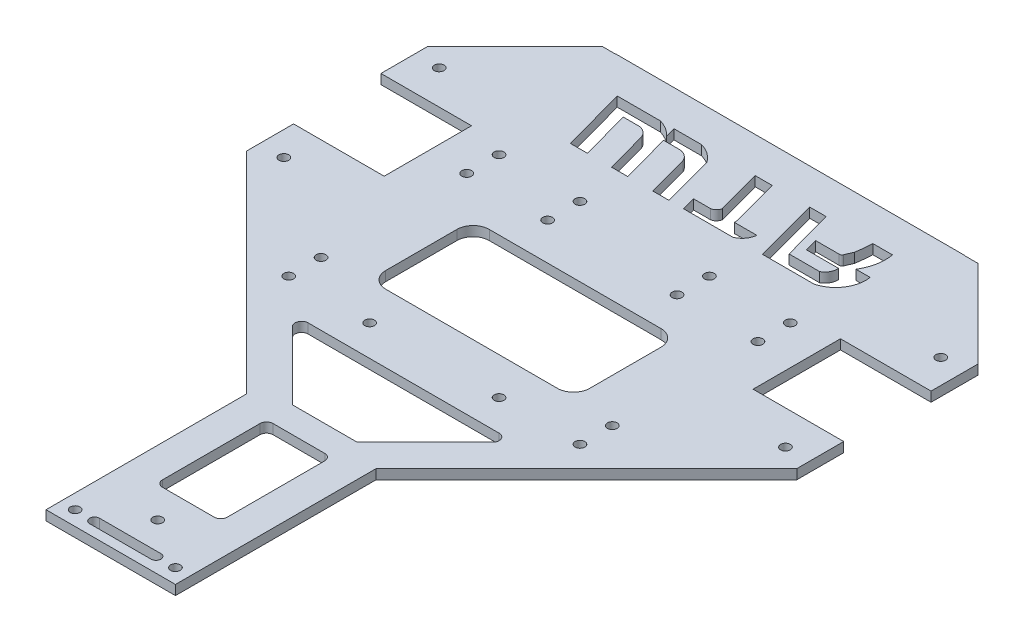
SolidWorks part; units mm, degrees
ref_plane "前视基准面" through (0, 0, 0) normal (0, 0, 1) x (1, 0, 0)
ref_plane "上视基准面" through (0, 0, 0) normal (0, 1, 0) x (1, 0, 0)
ref_plane "右视基准面" through (0, 0, 0) normal (1, 0, 0) x (0, 0, -1)
sketch "草图1" plane through (0, 0, 0) normal (0, 1, 0) x (1, 0, 0)
  line L0 (85, -28) -> (58, -55)
  line L1 (-85, -24) -> (85, -24)
  line L2 (-85, -24) -> (-85, 24)
  line L3 (-85, 24) -> (85, 24)
  line L4 (85, -24) -> (85, 24)
  line L5 (-85, -24) -> (85, 24) construction
  line L6 (-85, 24) -> (85, -24) construction
  line L7 (85, 13.5) -> (57, 13.5)
  line L8 (85, 13.5) -> (85, -13.5)
  line L9 (85, -13.5) -> (57, -13.5)
  line L10 (57, 13.5) -> (57, -13.5)
  line L11 (58, -55) -> (-58, -55)
  line L12 (0, -60) -> (0, 24)
  line L13 (65, 13.5) -> (65, -13.5)
  line L14 (85, 18.6302) -> (50, 18.6302)
  line L15 (50, 18.6302) -> (-50, 18.6302)
  line L16 (-85, -24) -> (-85, -28)
  line L17 (-85, -13.5) -> (-57, -13.5)
  line L18 (-57, 13.5) -> (-57, -13.5)
  line L19 (-65, 13.5) -> (-65, -13.5)
  line L20 (-85, 13.5) -> (-57, 13.5)
  line L21 (-85, 18.6302) -> (-50, 18.6302)
  line L22 (0, 0) -> (27.7736, 0)
  line L23 (85, -24) -> (85, -28)
  line L24 (-85, -28) -> (-58, -55)
  line L25 (85, 13.5) -> (85, 28)
  line L26 (85, 28) -> (85, 55)
  line L27 (85, 55) -> (-85, 55)
  line L28 (-85, 55) -> (-85, 24)
  line L29 (-85, 24) -> (-54, 55)
  line L30 (85, 24) -> (54, 55)
  circle A2 centre (77.5, 24) radius 1.5
  circle A3 centre (77.5, -24) radius 1.5
  circle A4 centre (-77.5, -24) radius 1.5
  circle A5 centre (-77.5, 24) radius 1.5
  point P0 (0, 0)
  point P34 (0, 18.6302)
  point P38 (85, 0)
  point P42 (0, -55)
  dimension "D4" = 3
  dimension "D5" = 7.5
  dimension "D7" = 7.5
  dimension "D8" = 3
  dimension "D1" = 48
  dimension "D2" = 27
  dimension "D3" = 28
  dimension "D6" = 10.5
  dimension "D9" = 20
  dimension "D10" = 35
  dimension "D11" = 50
  dimension "D12" = 45
  dimension "D13" = 55
  dimension "D14" = 28
  dimension "D15" = 28
  dimension "D16" = 55
  dimension "D17" = 45
extrude "凸台-拉伸1" add sketch "草图1" along normal blind 3
sketch "草图2" plane through (0, 3, 0) normal (0, 1, 0) x (1, 0, 0)
  line L0 (0, 0) -> (85, 0)
  line L1 (85, 0) -> (85, 28)
  line L2 (85, 28) -> (58.0785, 54.9215)
  line L3 (58.0785, 54.9215) -> (-58.0785, 54.9215)
  line L4 (-58.0785, 54.9215) -> (-85, 28)
  line L5 (-85, 28) -> (-85, 0)
  line L6 (-85, 0) -> (0, 0)
  line L7 (85, 13.5) -> (-85, 13.5)
  line L8 (-85, 13.5) -> (-57, 13.5) construction
  line M12 (57, 13.5) -> (85, 13.5)
  line M13 (85, 13.5) -> (85, 24)
  line M14 (85, 24) -> (54, 55)
  line M16 (-54, 55) -> (-85, 24)
  line M17 (-85, 24) -> (-85, 13.5)
  line M18 (-85, 13.5) -> (-57, 13.5)
  circle M24 centre (-77.5, 24) radius 1.5
  circle M25 centre (77.5, 24) radius 1.5
  dimension "D1" = 28
  dimension "D2" = 28
  dimension "D3" = 45
  dimension "D4" = 45
extrude "凸台-拉伸2" add sketch "草图2" against normal blind 3 contours L7 L3 M12 M13 M14 M16 M17 M18 M24 M25 | L4 L5 L3 M16 | L2 L3 L1 M14
sketch "草图3" plane through (0, 0, 0) normal (0, -1, 0) x (1, 0, 0)
  line L0 (-58, 55) -> (-58, 155)
  line L1 (-58, 155) -> (58, 155)
  line L2 (58, 155) -> (58, 55)
  line L3 (58, 55) -> (-58, 55) construction
  line L4 (58, 155) -> (-58, 55)
  line L5 (0, 55) -> (20, 55)
  line L6 (20, 55) -> (-20, 55)
  line L7 (20, 55) -> (20, 155)
  line L8 (20, 155) -> (-20, 155)
  line L9 (-20, 155) -> (-20, 55)
  line L10 (58, 55) -> (20, 93)
  line L11 (58, 55) -> (-58, 55) construction
  line L12 (-58, 55) -> (-20, 93)
  line M19 (58, 55) -> (-58, 55)
  dimension "D1" = 100
  dimension "D2" = 20
  dimension "D3" = 20
  dimension "D4" = 45
  dimension "D5" = 45
extrude "凸台-拉伸6" add sketch "草图3" against normal blind 3 contours L1 L9 L4 L7 | L4 L9 L7 M19 | L10 L7 M19 | L9 L4 M19 | L12 L4 L9
sketch "草图4" plane through (0, 0, 0) normal (0, -1, 0) x (1, 0, 0)
  line L0 (37.8771, -32.0433) -> (27.9672, -32.0433)
  line L1 (26.9205, -35.9371) -> (34.1003, -35.9371)
  line L2 (-11.551, -24.043) -> (-14.9813, -36.8035)
  line L3 (27.9672, -32.0433) -> (26.9205, -35.9371)
  line L4 (0.1789, -43.9838) -> (3.9173, -30.0769)
  line L5 (22.3759, -24.043) -> (17.0154, -43.9838)
  line L6 (-19.2517, -24.043) -> (-23.4468, -39.272)
  line L7 (-24.2571, -24.043) -> (-27.7723, -36.8035)
  line L8 (34.9825, -36.4576) -> (36.0132, -38.8388)
  line L9 (22.1349, -43.9838) -> (26.362, -28.2592)
  line L10 (40.7942, -34.4998) -> (45.1749, -34.4998)
  line L11 (36.5091, -43.9838) -> (42.602, -43.9838)
  line L12 (-42.4747, -43.9838) -> (-29.0805, -43.9838)
  line L13 (9.4351, -28.2592) -> (16.3934, -28.2592)
  line L14 (0.1789, -43.9838) -> (5.4498, -43.9838)
  line L15 (-23.4468, -39.272) -> (-18.2716, -39.272)
  line L16 (-3.1286, -28.2592) -> (2.1385, -28.2592)
  line L17 (-3.1286, -28.2592) -> (-1.9952, -24.043)
  line L18 (-6.5456, -24.043) -> (-10.8431, -40.0297)
  line L19 (-24.9419, -43.9838) -> (-24.0966, -40.9153)
  line L20 (-1.9952, -24.043) -> (13.1558, -24.043)
  line L21 (5.4498, -43.9838) -> (9.4351, -29.159)
  line L22 (22.3759, -24.043) -> (38.3377, -24.043)
  line L23 (9.4351, -28.2592) -> (9.4351, -29.159)
  line L24 (-24.9419, -43.9838) -> (-16.4388, -43.9838)
  line L25 (-11.551, -24.043) -> (-6.5456, -24.043)
  line L26 (26.362, -28.2592) -> (35.7851, -28.2592)
  line L27 (-36.9816, -24.043) -> (-31.7142, -24.043)
  line L28 (-35.9094, -39.272) -> (-30.8451, -39.272)
  line L29 (-31.7142, -24.043) -> (-35.9094, -39.272)
  line L30 (-24.2571, -24.043) -> (-19.2517, -24.043)
  line L31 (17.0154, -43.9838) -> (22.1349, -43.9838)
  line L32 (-36.9816, -24.043) -> (-42.4747, -43.9838)
  arc A0 (36.0132, -38.8388) -> (36.5091, -43.9838) centre (-5.4028, -45.4274) cw
  arc A1 (13.1558, -24.043) -> (16.3934, -28.2592) centre (11.3834, -28.7552) cw
  arc A2 (37.8771, -32.0433) -> (35.7851, -28.2592) centre (33.967, -31.7346) ccw
  arc A3 (-18.2716, -39.272) -> (-14.9813, -36.8035) centre (-18.7431, -35.2164) ccw
  arc A4 (34.9825, -36.4576) -> (34.1003, -35.9371) centre (34.1839, -36.8033) ccw
  arc A5 (-16.4388, -43.9838) -> (-10.8431, -40.0297) centre (-18.8304, -34.6629) ccw
  arc A6 (38.3377, -24.043) -> (45.1749, -34.4998) centre (35.9436, -33.0721) cw
  arc A7 (-30.8451, -39.272) -> (-27.7723, -36.8035) centre (-31.4815, -35.333) ccw
  arc A8 (42.602, -43.9838) -> (40.7942, -34.4998) centre (29.3345, -41.5985) ccw
  arc A9 (2.1385, -28.2592) -> (3.9173, -30.0769) centre (1.7187, -30.4494) cw
  arc A10 (-29.0805, -43.9838) -> (-24.0966, -40.9153) centre (-32.4014, -33.0082) ccw
extrude "切除-拉伸1" cut sketch "草图4" against normal blind 3
sketch "草图5" plane through (0, 0, 0) normal (0, -1, 0) x (1, 0, 0)
  line L0 (0, 0) -> (45, 0)
  line L1 (45, 0) -> (45, 55)
  line L2 (45, 55) -> (-45, 55)
  line L3 (-45, 55) -> (-45, 0)
  line L4 (-45, 0) -> (0, 0)
  line L5 (-20, 93) -> (-20, 55)
  line L6 (20, 93) -> (20, 55)
  line L7 (45, 0) -> (45, 45)
  line L8 (45, 45) -> (-45, 45)
  line L9 (-57, -13.5) -> (-57, 13.5) construction
  line L10 (-85, 28) -> (-85, 13.5) construction
  line L11 (45, 0) -> (45, -10)
  line L12 (-45, 0) -> (-45, -10)
  line L13 (20, 55) -> (20, 0)
  line L14 (20, 0) -> (-20, 0)
  line L15 (45, -10) -> (-45, -10)
  line L16 (-20, 0) -> (-20, -10)
  line L17 (-20, -10) -> (20, -10)
  circle A0 centre (45, 55) radius 1.5
  circle A1 centre (-45, 55) radius 1.5
  circle A2 centre (20, 55) radius 1.5
  circle A3 centre (-20, 55) radius 1.5
  circle A4 centre (45, 45) radius 1.5
  circle A5 centre (-45, 45) radius 1.5
  circle A6 centre (-45, 0) radius 1.5
  circle A7 centre (45, 0) radius 1.5
  circle A8 centre (45, -10) radius 1.5
  circle A9 centre (-45, -10) radius 1.5
  circle A10 centre (20, 0) radius 1.5
  circle A11 centre (-20, 0) radius 1.5
  circle A12 centre (20, -10) radius 1.5
  circle A13 centre (-20, -10) radius 1.5
  dimension "D4" = 3
  dimension "D5" = 3
  dimension "D6" = 3
  dimension "D7" = 3
  dimension "D9" = 3
  dimension "D10" = 3
  dimension "D13" = 3
  dimension "D14" = 3
  dimension "D17" = 3
  dimension "D18" = 3
  dimension "D19" = 3
  dimension "D20" = 3
  dimension "D21" = 3
  dimension "D22" = 3
  dimension "D1" = 55
  dimension "D2" = 45
  dimension "D3" = 45
  dimension "D8" = 45
  dimension "D11" = 12
  dimension "D12" = 40
  dimension "D15" = 10
  dimension "D16" = 10
extrude "切除-拉伸2" cut sketch "草图5" against normal blind 3 contours A1 | A5 | A3 | A2 | A0 | A4 | A7 | A8 | A12 | A10 | A11 | A13 | A9 | A6
sketch "草图6" plane through (0, 0, 0) normal (0, -1, 0) x (1, 0, 0)
  line L0 (-20, 155) -> (20, 155)
  line L1 (20, 155) -> (20, 93)
  line L2 (20, 93) -> (-20, 93)
  line L3 (-20, 93) -> (-20, 155)
  line L4 (-20, 155) -> (-20, 150.5)
  line L5 (-20, 150.5) -> (20, 150.5)
  line L6 (20, 150.5) -> (20, 140.5)
  line L7 (20, 140.5) -> (-20, 140.5)
  line L8 (-20, 140.5) -> (-20, 150.5)
  line L9 (20, 150.5) -> (15.5, 150.5)
  line L10 (0, 155) -> (0, 140.5)
  line L11 (15.5, 150.5) -> (9.5, 150.5)
  line L12 (9.5, 152) -> (-9.5, 152)
  line L13 (-9.5, 149) -> (9.5, 149)
  circle A0 centre (15.5, 150.5) radius 1.5
  circle A1 centre (0, 140.5) radius 1.5
  circle A2 centre (-15.5, 150.5) radius 1.5
  circle A3 centre (9.5, 150.5) radius 1.5
  circle A4 centre (-9.5, 150.5) radius 1.5
  dimension "D3" = 3
  dimension "D5" = 3
  dimension "D7" = 3
  dimension "D1" = 4.5
  dimension "D2" = 4.5
  dimension "D4" = 10
  dimension "D6" = 6
extrude "切除-拉伸5" cut sketch "草图6" against normal blind 3 contours L12 A4 L5 L10 | L5 A4 L13 L10 | A4 L5 | A4 L5 | A3 L12 L10 L5 | A3 L5 L10 L13 | A3 L5 | L5 A3 | A1 | A2 | A0
sketch "草图7" plane through (0, 0, 0) normal (0, -1, 0) x (1, 0, 0)
  line L0 (-12.093, 131) -> (8, 131)
  line L1 (0, 0) -> (0, 131)
  line L2 (10, 129) -> (10, 88.8579)
  line L3 (10, 88.8579) -> (30.9437, 67.9142)
  line L4 (29.5294, 64.5) -> (-29.5294, 64.5)
  line L5 (85, 28) -> (20, 93) construction
  line L6 (20, 93) -> (20, 155) construction
  line L7 (0, 139) -> (0, 131)
  line L8 (20, 56.5) -> (20, 64.5)
  line L9 (10, 88.8579) -> (-10, 88.8579)
  line L10 (0, 88.8579) -> (0, 96.8579)
  line L11 (-10, 96.8579) -> (10, 96.8579)
  line L12 (10, 96.8579) -> (10, 98.8579)
  line L13 (10, 98.8579) -> (8, 98.8579)
  line L14 (-10, 88.8579) -> (-30.9437, 67.9142)
  line L15 (-10, 129) -> (-10, 88.8579)
  line L16 (12.093, 131) -> (-8, 131)
  circle A0 centre (0, 140.5) radius 1.5 construction
  arc A1 (30.9437, 67.9142) -> (29.5294, 64.5) centre (29.5294, 66.5) cw
  circle A2 centre (20, 55) radius 1.5 construction
  arc A3 (8, 131) -> (10, 129) centre (8, 129) cw
  circle A4 centre (8, 98.8579) radius 2
  arc A5 (-30.9437, 67.9142) -> (-29.5294, 64.5) centre (-29.5294, 66.5) ccw
  circle A6 centre (-8, 98.8579) radius 2
  arc A7 (-8, 131) -> (-10, 129) centre (-8, 129) ccw
  point P30 (0, 64.5)
  dimension "D3" = 8
  dimension "D6" = 2
  dimension "D1" = 10
  dimension "D2" = 10
  dimension "D4" = 8
  dimension "D5" = 8
  dimension "D7" = 2
extrude "切除-拉伸7" cut sketch "草图7" against normal blind 3
sketch "草图8" plane through (0, 0, 0) normal (0, -1, 0) x (1, 0, 0)
  line L0 (0, 0) -> (0, 31.431)
  line L1 (24.5611, 74.2968) -> (36.4558, 62.402)
  line L2 (10, 88.8579) -> (30.9437, 67.9142) construction
  line L3 (29.5294, 64.5) -> (-29.5294, 64.5) construction
  line L4 (9.3176, 64.5) -> (40.1117, 64.5)
  line L5 (31.5294, 38.5) -> (31.5294, 16.5)
  line L6 (26.5294, 11.5) -> (-26.5294, 11.5)
  line L7 (-33.7935, 11.5) -> (-33.7935, 43.5)
  line L8 (-26.5294, 43.5) -> (26.5294, 43.5)
  line L9 (20, 53.5) -> (20, 43.5)
  line L10 (20, 1.5) -> (20, 11.5)
  line L11 (20, 43.5) -> (31.5294, 43.5)
  line L12 (43.5, 45) -> (31.5294, 45)
  line L13 (-31.5294, 38.5) -> (-31.5294, 16.5)
  circle A1 centre (20, 55) radius 1.5 construction
  circle A2 centre (20, 0) radius 1.5 construction
  circle A3 centre (45, 45) radius 1.5 construction
  arc A5 (26.5294, 43.5) -> (31.5294, 38.5) centre (26.5294, 38.5) cw
  arc A6 (31.5294, 16.5) -> (26.5294, 11.5) centre (26.5294, 16.5) cw
  arc A7 (-31.5294, 16.5) -> (-26.5294, 11.5) centre (-26.5294, 16.5) ccw
  arc A8 (-31.5294, 38.5) -> (-26.5294, 43.5) centre (-26.5294, 38.5) cw
  point P11 (34.3579, 64.5)
  dimension "D3" = 5
  dimension "D1" = 10
  dimension "D2" = 10
extrude "切除-拉伸9" cut sketch "草图8" against normal blind 3
